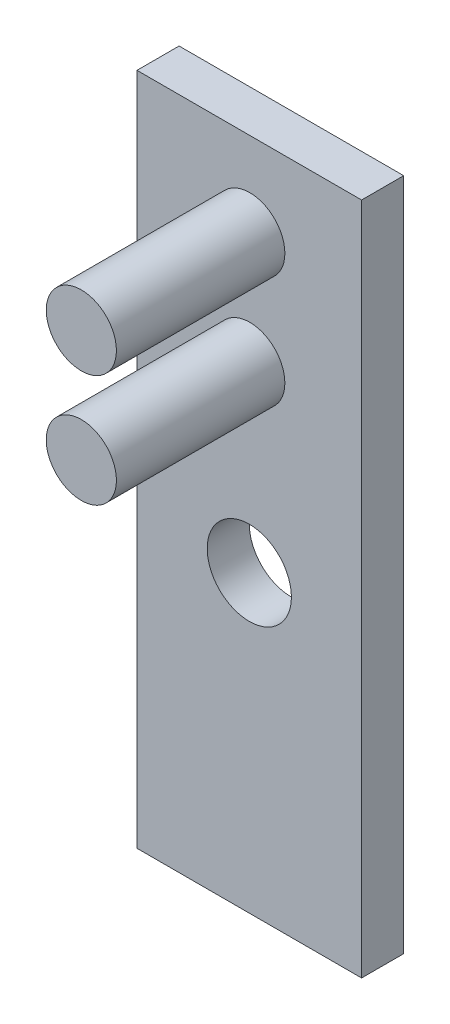
SolidWorks part; units mm, degrees
ref_plane "Front Plane" through (0, 0, 0) normal (0, 0, 1) x (1, 0, 0)
ref_plane "Top Plane" through (0, 0, 0) normal (0, 1, 0) x (1, 0, 0)
ref_plane "Right Plane" through (0, 0, 0) normal (1, 0, 0) x (0, 0, -1)
sketch "Sketch1" plane through (0, 0, 0) normal (0, 0, 1) x (1, 0, 0)
  line L1 (-15.9825, 8.954) -> (-7.9825, 8.954)
  line L2 (-15.9825, 8.954) -> (-15.9825, -15.046)
  line L3 (-15.9825, -15.046) -> (-7.9825, -15.046)
  line L4 (-7.9825, 8.954) -> (-7.9825, -15.046)
  dimension "D1" = 24
  dimension "D2" = 8
extrude "Boss-Extrude1" add sketch "Sketch1" along normal blind 1.5
sketch "Sketch2" plane through (0, 0, 1.5) normal (0, 0, 1) x (1, 0, 0)
  line L0 (-7.9825, 8.954) -> (-15.9825, 8.954) construction
  circle A0 centre (-11.9825, -4.546) radius 1.5
  point P6 (-11.9825, 8.954)
  dimension "D1" = 3
  dimension "D2" = 13.5
extrude "Cut-Extrude1" cut sketch "Sketch2" against normal through all contours A0
sketch "Sketch3" plane through (0, 0, 1.5) normal (0, 0, 1) x (1, 0, 0)
  line L1 (-15.5201, 8.4403) -> (-8.5201, 8.4403)
  line L2 (-15.5201, 8.4403) -> (-15.5201, -0.5597)
  line L3 (-15.5201, -0.5597) -> (-8.5201, -0.5597)
  line L4 (-8.5201, 8.4403) -> (-8.5201, -0.5597)
  line L5 (-15.1201, 8.0403) -> (-8.9201, 8.0403)
  line L6 (-15.1201, 8.0403) -> (-15.1201, -0.1597)
  line L7 (-15.1201, -0.1597) -> (-8.9201, -0.1597)
  line L8 (-8.9201, 8.0403) -> (-8.9201, -0.1597)
  circle A0 centre (-11.9657, 5.9403) radius 1.25
  circle A1 centre (-11.9657, 1.9403) radius 1.25
  dimension "D2" = 2.5
  dimension "D3" = 2.5
  dimension "2.5" = 2.5
  dimension "D1" = 9
  dimension "7" = 7
  dimension "3" = 2.5
  dimension "D4" = 0.4
  dimension "D5" = 0.4
  dimension "0.4" = 0.4
  dimension "D6" = 0.4
extrude "Boss-Extrude3" add sketch "Sketch3" along normal blind 6 contours A1 | A0
